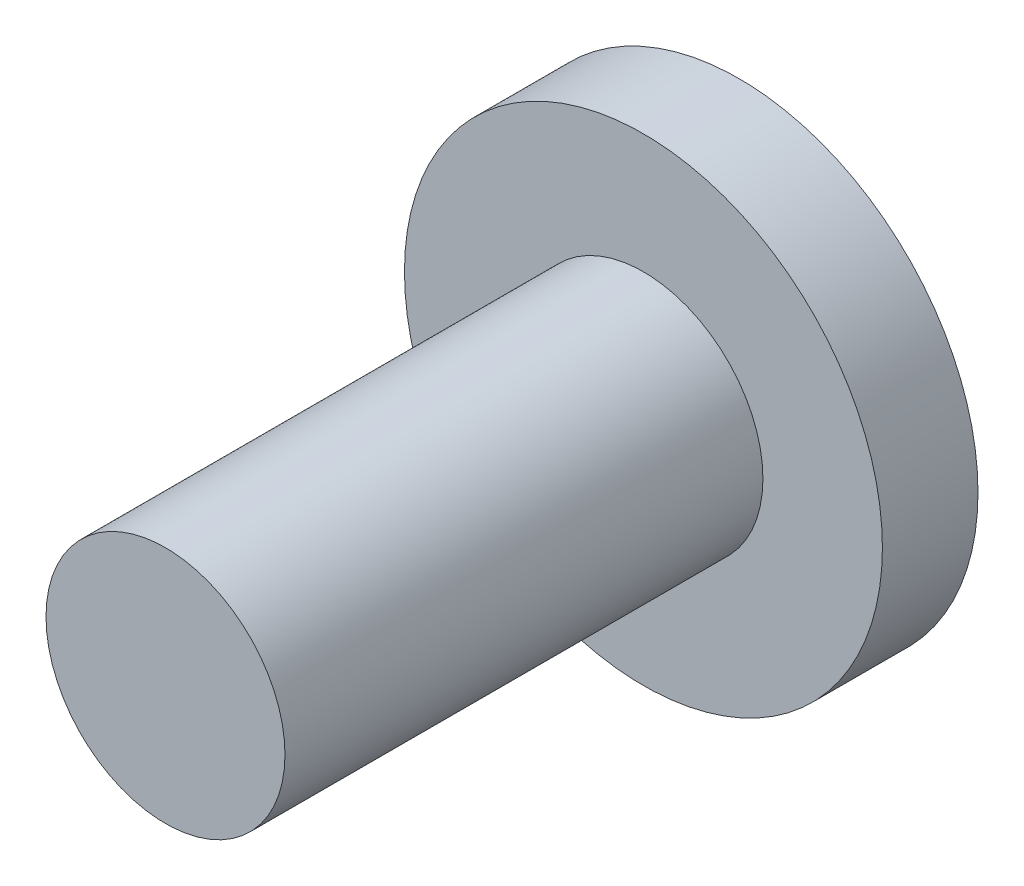
SolidWorks part; units mm, degrees
ref_plane "Front Plane" through (0, 0, 0) normal (0, 0, 1) x (1, 0, 0)
ref_plane "Top Plane" through (0, 0, 0) normal (0, 1, 0) x (1, 0, 0)
ref_plane "Right Plane" through (0, 0, 0) normal (1, 0, 0) x (0, 0, -1)
sketch "Sketch1" plane through (0, 0, 0) normal (0, 0, 1) x (1, 0, 0)
  circle A0 centre (0, 0) radius 2
  dimension "D1" = 4
extrude "Boss-Extrude1" add sketch "Sketch1" along normal blind 0.8
sketch "Sketch2" plane through (0, 0, 0.8) normal (0, 0, 1) x (1, 0, 0)
  circle A0 centre (0, 0) radius 1
  dimension "D1" = 2
extrude "Boss-Extrude2" add sketch "Sketch2" along normal blind 4
